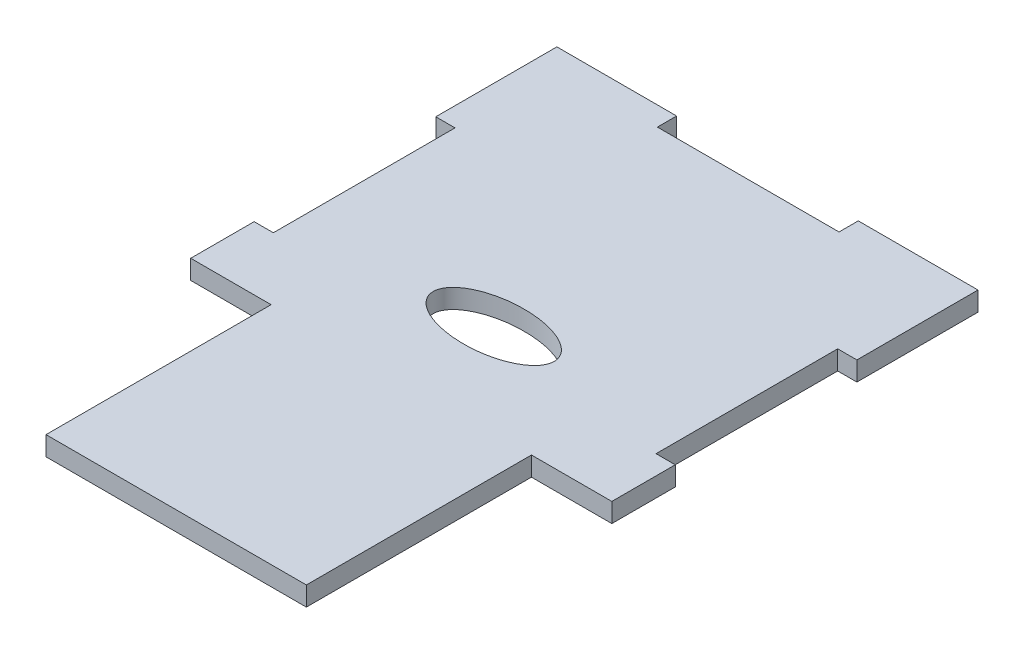
SolidWorks part; units mm, degrees
ref_plane "Front Plane" through (0, 0, 0) normal (0, 0, 1) x (1, 0, 0)
ref_plane "Top Plane" through (0, 0, 0) normal (0, 1, 0) x (1, 0, 0)
ref_plane "Right Plane" through (0, 0, 0) normal (1, 0, 0) x (0, 0, -1)
sketch "Sketch1" plane through (0, 0, 0) normal (0, 1, 0) x (1, 0, 0)
  line L0 (19.775, 91.3) -> (19.775, 94.475)
  line L1 (0, 0) -> (69.55, 0)
  line L2 (0, 0) -> (0, 94.475)
  line L3 (0, 94.475) -> (69.55, 94.475)
  line L4 (69.55, 0) -> (69.55, 94.475)
  line L5 (0, 0) -> (13.275, 0)
  line L6 (0, 0) -> (0, 34)
  line L7 (0, 34) -> (13.275, 34)
  line L8 (13.275, 0) -> (13.275, 34)
  line L9 (69.55, 0) -> (56.275, 0)
  line L10 (69.55, 0) -> (69.55, 34)
  line L11 (69.55, 34) -> (56.275, 34)
  line L12 (56.275, 0) -> (56.275, 34)
  line L13 (19.775, 91.3) -> (49.775, 91.3)
  line L14 (19.775, 94.475) -> (49.775, 94.475)
  line L15 (49.775, 91.3) -> (49.775, 94.475)
  line L16 (19.775, 91.3) -> (49.775, 94.475) construction
  line L17 (19.775, 94.475) -> (49.775, 91.3) construction
  line L19 (13.275, 0) -> (56.275, 0)
  line L20 (13.275, 0) -> (13.275, -3.175)
  line L21 (13.275, -3.175) -> (56.275, -3.175)
  line L22 (56.275, 0) -> (56.275, -3.175)
  line L23 (3.175, 44.475) -> (0, 44.475)
  line L24 (3.175, 44.475) -> (3.175, 74.475)
  line L25 (3.175, 74.475) -> (0, 74.475)
  line L26 (0, 44.475) -> (0, 74.475)
  line L27 (3.175, 44.475) -> (0, 74.475) construction
  line L28 (3.175, 74.475) -> (0, 44.475) construction
  line L29 (66.375, 74.475) -> (69.55, 74.475)
  line L30 (66.375, 74.475) -> (66.375, 44.475)
  line L31 (66.375, 44.475) -> (69.55, 44.475)
  line L32 (69.55, 74.475) -> (69.55, 44.475)
  line L33 (66.375, 74.475) -> (69.55, 44.475) construction
  line L34 (66.375, 44.475) -> (69.55, 74.475) construction
  ellipse E0 centre (34.775, 49.2713) end of major axis (24.775, 49.2713) minor radius 5
  point P18 (34.775, 94.475)
  point P19 (34.775, 92.8875)
  point P21 (1.5875, 59.475)
  point P30 (67.9625, 59.475)
  point P35 (0, 0)
  dimension "D1" = 69.55
  dimension "D2" = 94.475
  dimension "D3" = 34
  dimension "D4" = 43
  dimension "D5" = 10
  dimension "D6" = 20
  dimension "D7" = 3.175
  dimension "D8" = 30
  dimension "D9" = 3.175
  dimension "D10" = 3.175
  dimension "D11" = 30
  dimension "D12" = 20
extrude "Boss-Extrude1" add sketch "Sketch1" along normal blind 3.175 contours L1 L12 L11 L4 L3 L2 L7 L8 | L22 L1 L20 L21
